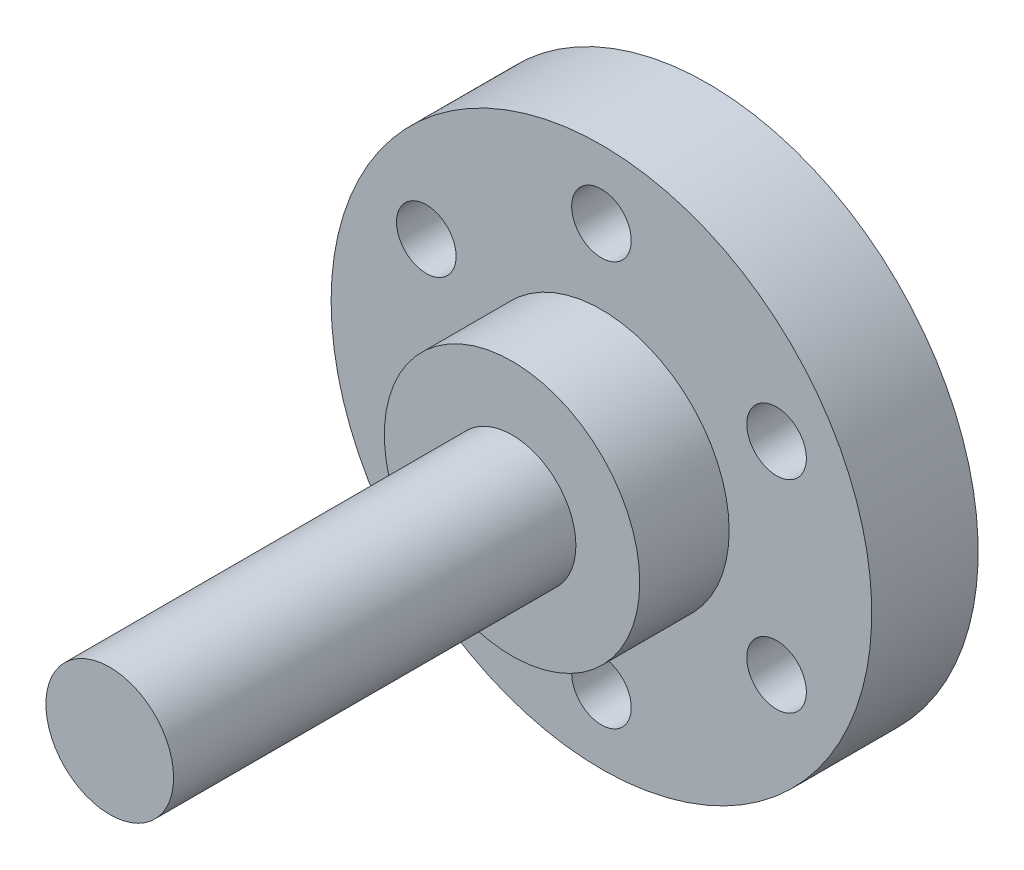
SolidWorks part; units mm, degrees
material "1060 Alloy"
ref_plane "Front Plane" through (0, 0, 0) normal (0, 0, 1) x (1, 0, 0)
ref_plane "Top Plane" through (0, 0, 0) normal (0, 1, 0) x (1, 0, 0)
ref_plane "Right Plane" through (0, 0, 0) normal (1, 0, 0) x (0, 0, -1)
sketch "Sketch1" plane through (0, 0, 0) normal (0, 0, 1) x (1, 0, 0)
  circle A0 centre (0, 0) radius 3
  dimension "D1" = 6
extrude "Boss-Extrude1" add sketch "Sketch1" along normal blind 29
ref_plane "Plane1" through (0, 0, 8) normal (0, 0, 1) x (1, 0, 0)
sketch "Sketch2" plane through (0, 0, 8) normal (0, 0, 1) x (1, 0, 0)
  circle A0 centre (0, 0) radius 6
  dimension "D1" = 12
  dimension "D2" = 12
extrude "Boss-Extrude2" add sketch "Sketch2" against normal blind 2.1
sketch "Sketch3" plane through (0, 0, 5.9) normal (0, 0, -1) x (-1, 0, 0)
  circle A0 centre (0, 0) radius 12.7
  dimension "D1" = 25.4
extrude "Boss-Extrude3" add sketch "Sketch3" along normal blind 5
sketch "Sketch4" plane through (0, 0, 8) normal (0, 0, 1) x (1, 0, 0)
  circle A0 centre (0, 0) radius 6
extrude "Boss-Extrude4" add sketch "Sketch4" along normal blind 2.1
sketch "Sketch10" plane through (0, 0, 0.9) normal (0, 0, -1) x (-1, 0, 0)
  circle A0 centre (8.2272, 4.75) radius 1.4
  circle A1 centre (0, 9.5) radius 1.4
  circle A2 centre (8.2272, -4.75) radius 1.4
  circle A3 centre (0, -9.5) radius 1.4
  circle A4 centre (-8.2272, -4.75) radius 1.4
  circle A5 centre (-8.2272, 4.75) radius 1.4
  point P15 (0, 0)
  dimension "D1" = 6
  dimension "D2" = 2.8
extrude "Cut-Extrude1" cut sketch "Sketch10" against normal blind 5
